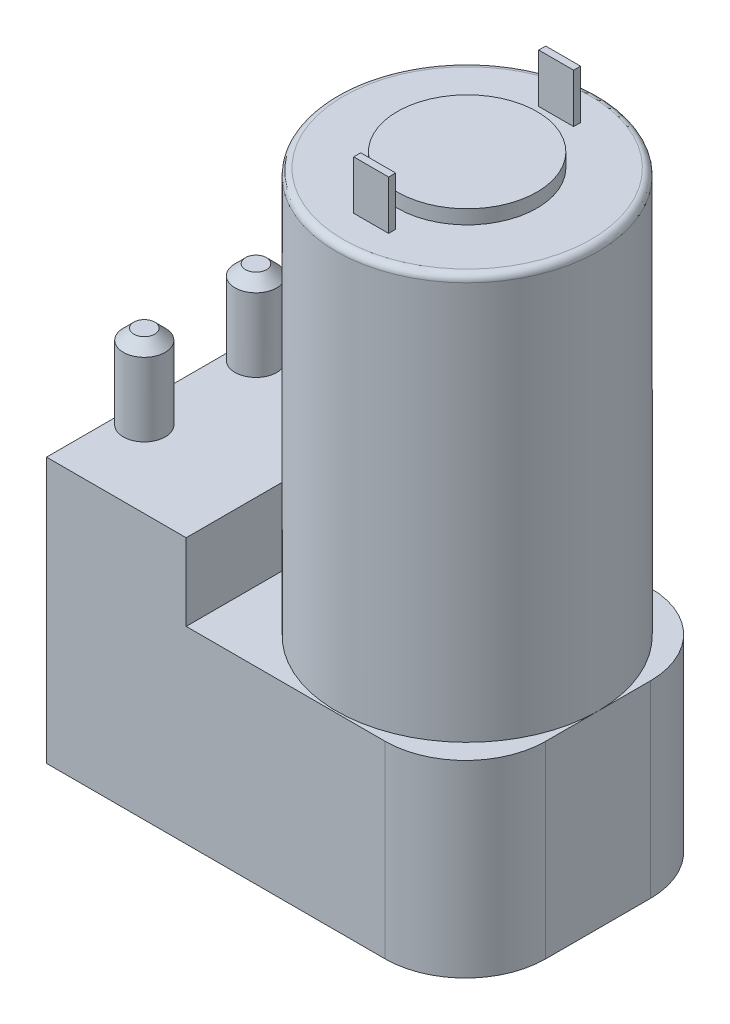
SolidWorks part; units mm, degrees
ref_plane "Face" through (0, 0, 0) normal (0, 0, 1) x (1, 0, 0)
ref_plane "Dessus" through (0, 0, 0) normal (0, 1, 0) x (1, 0, 0)
ref_plane "Droite" through (0, 0, 0) normal (1, 0, 0) x (0, 0, -1)
sketch "Esquisse1" plane through (0, 0, 0) normal (0, 1, 0) x (1, 0, 0)
  line L0 (0, 0) -> (48.5, 0)
  line L1 (0, 0) -> (0, 38)
  line L2 (0, 38) -> (48.5, 38)
  line L3 (60, 26.5) -> (60, 11.5)
  line L4 (60, 19) -> (0, 19) construction
  arc A0 (48.5, 38) -> (60, 26.5) centre (48.5, 26.5) cw
  arc A1 (60, 11.5) -> (48.5, 0) centre (48.5, 11.5) cw
  dimension "D1" = 38
  dimension "D2" = 60
  dimension "D3" = 15
extrude "Extrusion1" add sketch "Esquisse1" along normal blind 27
sketch "Esquisse2" plane through (0, 27, 0) normal (0, 1, 0) x (1, 0, 0)
  line L0 (0, 38) -> (0, 0)
  line L1 (0, 0) -> (20, 0)
  line L2 (0, 0) -> (48.5, 0) construction
  line L3 (20, 0) -> (20, 38)
  line L4 (48.5, 38) -> (0, 38) construction
  line L5 (20, 38) -> (0, 38)
  dimension "D1" = 20
extrude "Extrusion2" add sketch "Esquisse2" along normal blind 11
sketch "Esquisse3" plane through (0, 27, 0) normal (0, 1, 0) x (1, 0, 0)
  line L0 (60, 19) -> (20, 19) construction
  line L1 (60, 11.5) -> (60, 26.5) construction
  line L2 (20, 0) -> (20, 38) construction
  circle A0 centre (41.25, 19) radius 18.75
  dimension "D1" = 37.5
extrude "Extrusion3" add sketch "Esquisse3" along normal blind 58
sketch "Esquisse4" plane through (0, 85, 0) normal (0, 1, 0) x (1, 0, 0)
  circle A0 centre (41.25, 19) radius 10
  dimension "D1" = 20
extrude "Extrusion4" add sketch "Esquisse4" along normal blind 2
sketch "Esquisse5" plane through (0, 38, 0) normal (0, 1, 0) x (1, 0, 0)
  line L0 (3, 38) -> (3, 0) construction
  line L1 (20, 38) -> (0, 38) construction
  line L2 (0, 0) -> (20, 0) construction
  line L3 (0, 19) -> (20, 19) construction
  line L4 (0, 38) -> (0, 0) construction
  line L5 (20, 0) -> (20, 38) construction
  circle A0 centre (3, 27) radius 3
  circle A1 centre (3, 11) radius 3
  dimension "D1" = 6
  dimension "D2" = 8
extrude "Extrusion5" add sketch "Esquisse5" along normal blind 12
chamfer "Chanfrein1" distance 1.5 angle 45 2 edges at (3, 50, -14) (3, 50, -24)
fillet "Congé1" radius 1 1 edges at (41.25, 85, -0.25)
sketch "Esquisse6" plane through (0, 85, 0) normal (0, 1, 0) x (1, 0, 0)
  line L0 (41.25, 36.75) -> (41.25, 1.25) construction
  line L1 (23.5, 19) -> (59, 19) construction
  line L2 (43.75, 32.75) -> (38.75, 32.75)
  line L3 (38.75, 32.75) -> (38.75, 31.75)
  line L4 (38.75, 31.75) -> (43.75, 31.75)
  line L5 (43.75, 32.75) -> (43.75, 31.75)
  line L6 (43.75, 5.25) -> (43.75, 6.25)
  line L7 (43.75, 5.25) -> (38.75, 5.25)
  line L8 (38.75, 5.25) -> (38.75, 6.25)
  line L9 (38.75, 6.25) -> (43.75, 6.25)
  circle A0 centre (41.25, 19) radius 17.75 construction
  point P12 (41.25, 31.75)
  point P13 (41.25, 32.75)
  dimension "D3" = 5
  dimension "D1" = 1
  dimension "D2" = 2.5
extrude "Extrusion6" add sketch "Esquisse6" along normal blind 7
